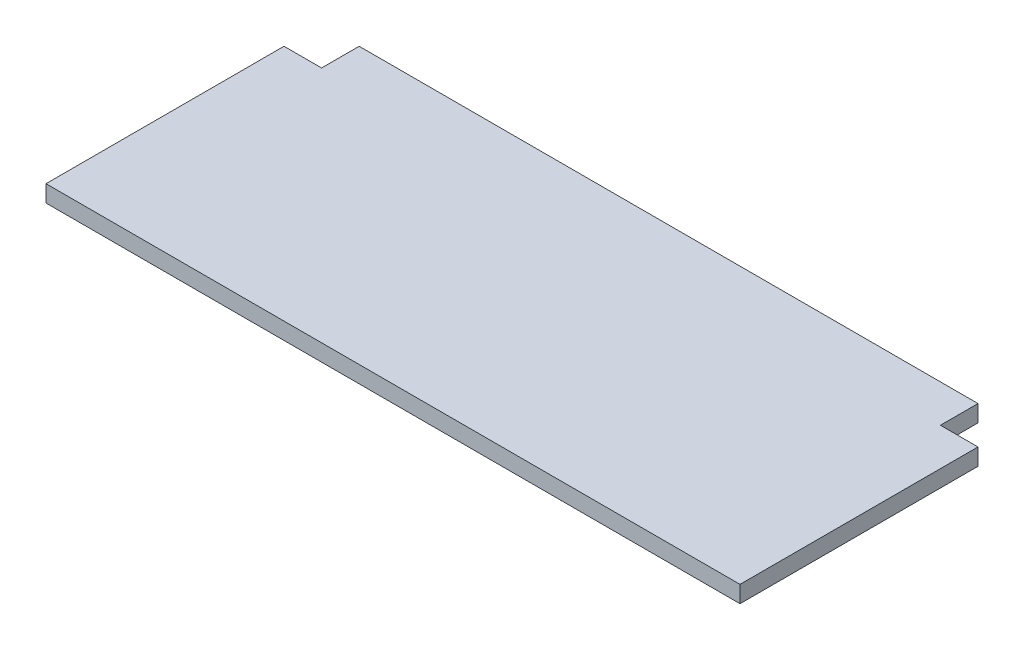
SolidWorks part; units mm, degrees
ref_plane "Front Plane" through (0, 0, 0) normal (0, 0, 1) x (1, 0, 0)
ref_plane "Top Plane" through (0, 0, 0) normal (0, 1, 0) x (1, 0, 0)
ref_plane "Right Plane" through (0, 0, 0) normal (1, 0, 0) x (0, 0, -1)
sketch "Sketch1" plane through (0, 0, 0) normal (0, 1, 0) x (1, 0, 0)
  line L1 (-351.79, -139.7) -> (351.79, -139.7)
  line L2 (-351.79, -139.7) -> (-351.79, 101.6)
  line L3 (-313.69, 139.7) -> (313.69, 139.7)
  line L4 (351.79, -139.7) -> (351.79, 101.6)
  line L5 (-351.79, -139.7) -> (351.79, 139.7) construction
  line L6 (-351.79, 139.7) -> (351.79, -139.7) construction
  line L9 (-351.79, 101.6) -> (-313.69, 101.6)
  line L10 (-313.69, 139.7) -> (-313.69, 101.6)
  line L13 (351.79, 101.6) -> (313.69, 101.6)
  line L14 (313.69, 139.7) -> (313.69, 101.6)
  point P1 (0, 0)
  dimension "D1" = 703.58
  dimension "D2" = 279.4
  dimension "D3" = 38.1
  dimension "D4" = 38.1
  dimension "D5" = 38.1
  dimension "D6" = 38.1
extrude "Boss-Extrude2" add sketch "Sketch1" along normal blind 17.018
equation "\"D4@Sketch1\"=\"D3@Sketch1\""
